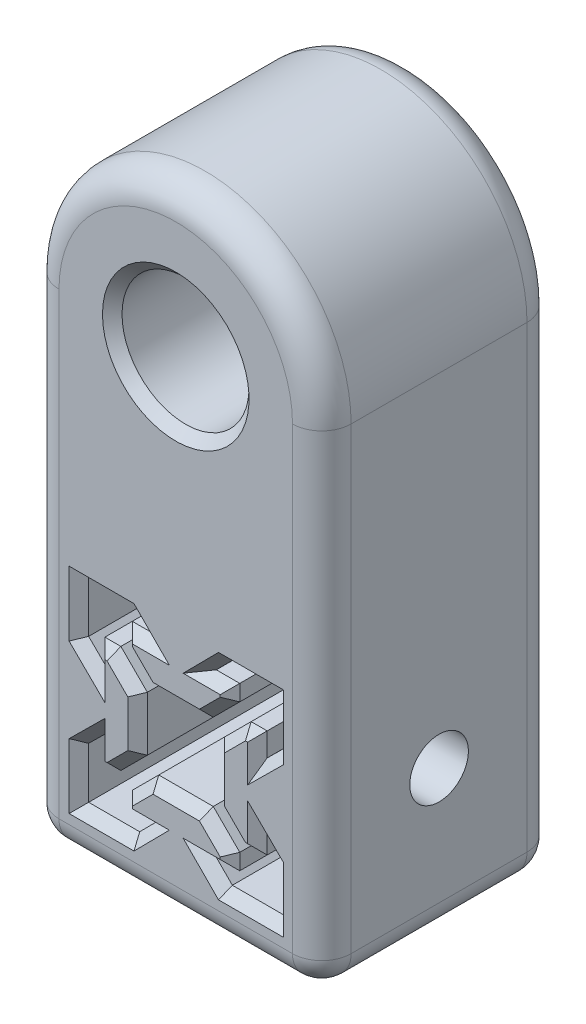
SolidWorks part; units mm, degrees
ref_plane "Front Plane" through (0, 0, 0) normal (0, 0, 1) x (1, 0, 0)
ref_plane "Top Plane" through (0, 0, 0) normal (0, 1, 0) x (1, 0, 0)
ref_plane "Right Plane" through (0, 0, 0) normal (1, 0, 0) x (0, 0, -1)
sketch "Sketch1" plane through (0, 0, 0) normal (0, 0, 1) x (1, 0, 0)
  line L0 (0, -15) -> (0, 15) construction
  line L1 (0, 15) -> (14.8993, 15)
  line L2 (14.8993, 15) -> (14.8993, -14.9496)
  line L3 (14.8993, -14.9496) -> (-15, -14.9496)
  line L4 (-15, -14.9496) -> (-15, 15)
  line L5 (-15, 15) -> (0, 15)
  line L6 (0, -9.9664) -> (0, 9.9664) construction
  line L7 (0, 9.9664) -> (-9.9664, 9.9664) construction
  line L8 (-9.9664, 9.9664) -> (-4.7414, 9.9664)
  line L9 (-4.7414, 9.9664) -> (-3.1, 8.3075)
  line L10 (-3.1, 8.3075) -> (0, 8.3075) construction
  line L11 (-3.1, 8.3075) -> (-5.5, 8.3075)
  line L12 (-5.5, 8.3075) -> (-5.5, 6.6675)
  line L13 (-5.5, 6.6675) -> (-2.79, 3.9575)
  line L14 (-2.79, 3.9575) -> (0, 3.9575) construction
  line L15 (-2.79, 3.9575) -> (2.79, 3.9575)
  line L16 (-9.9664, 9.9664) -> (0, 0) construction
  line L17 (-3.9575, 2.79) -> (-3.9575, -2.79)
  line L18 (-6.6675, 5.5) -> (-3.9575, 2.79)
  line L19 (-8.3075, 5.5) -> (-6.6675, 5.5)
  line L20 (-8.3075, 3.1) -> (-8.3075, 5.5)
  line L21 (-9.9664, 4.7414) -> (-8.3075, 3.1)
  line L22 (-9.9664, 9.9664) -> (-9.9664, 4.7414)
  line L23 (0, 0) -> (-11.0308, 0) construction
  line L24 (5.5, 6.6675) -> (2.79, 3.9575)
  line L25 (5.5, 8.3075) -> (5.5, 6.6675)
  line L26 (3.1, 8.3075) -> (5.5, 8.3075)
  line L27 (4.7414, 9.9664) -> (3.1, 8.3075)
  line L28 (9.9664, 9.9664) -> (4.7414, 9.9664)
  line L29 (9.9664, 9.9664) -> (9.9664, 4.7414)
  line L30 (9.9664, 4.7414) -> (8.3075, 3.1)
  line L31 (8.3075, 3.1) -> (8.3075, 5.5)
  line L32 (8.3075, 5.5) -> (6.6675, 5.5)
  line L33 (6.6675, 5.5) -> (3.9575, 2.79)
  line L34 (3.9575, 2.79) -> (3.9575, -2.79)
  line L35 (-9.9664, -9.9664) -> (0, 0) construction
  line L36 (-2.79, -3.9575) -> (0, -3.9575) construction
  line L37 (-3.1, -8.3075) -> (0, -8.3075) construction
  line L38 (0, -9.9664) -> (-9.9664, -9.9664) construction
  line L39 (6.6675, -5.5) -> (3.9575, -2.79)
  line L40 (8.3075, -5.5) -> (6.6675, -5.5)
  line L41 (8.3075, -3.1) -> (8.3075, -5.5)
  line L42 (9.9664, -4.7414) -> (8.3075, -3.1)
  line L43 (9.9664, -9.9664) -> (9.9664, -4.7414)
  line L44 (9.9664, -9.9664) -> (4.7414, -9.9664)
  line L45 (4.7414, -9.9664) -> (3.1, -8.3075)
  line L46 (3.1, -8.3075) -> (5.5, -8.3075)
  line L47 (5.5, -8.3075) -> (5.5, -6.6675)
  line L48 (5.5, -6.6675) -> (2.79, -3.9575)
  line L49 (-9.9664, -9.9664) -> (-9.9664, -4.7414)
  line L50 (-9.9664, -4.7414) -> (-8.3075, -3.1)
  line L51 (-8.3075, -3.1) -> (-8.3075, -5.5)
  line L52 (-8.3075, -5.5) -> (-6.6675, -5.5)
  line L53 (-6.6675, -5.5) -> (-3.9575, -2.79)
  line L54 (-2.79, -3.9575) -> (2.79, -3.9575)
  line L55 (-5.5, -6.6675) -> (-2.79, -3.9575)
  line L56 (-5.5, -8.3075) -> (-5.5, -6.6675)
  line L57 (-3.1, -8.3075) -> (-5.5, -8.3075)
  line L58 (-4.7414, -9.9664) -> (-3.1, -8.3075)
  line L59 (-9.9664, -9.9664) -> (-4.7414, -9.9664)
  point P43 (3.9575, 0)
  point P58 (-3.9575, 0)
  dimension "D1" = 3.1
  dimension "D2" = 2.79
  dimension "D3" = 2.4
  dimension "D4" = 135
  dimension "D5" = 1.64
  dimension "D6" = 15
  dimension "D7" = 15
  dimension "D8" = 9.9664
  dimension "D9" = 5.225
extrude "Boss-Extrude1" add sketch "Sketch1" along normal blind 24
sketch "Sketch4" plane through (0, 0, 0) normal (0, 0, -1) x (-1, 0, 0)
  line L0 (0.0504, 15) -> (0.0504, 28.5) construction
  line L1 (-14.8993, 15) -> (15, 15) construction
  line L2 (0.0504, 28.5) -> (0.0504, 35) construction
  line L3 (-14.8993, 15) -> (-14.8993, 35)
  line L4 (15, 35) -> (15, 15)
  line L5 (15, 15) -> (-14.8993, 15)
  line L6 (15, -14.9496) -> (-14.8993, -14.9496) construction
  circle A0 centre (0.0504, 35) radius 6.5
  arc A1 (-14.8993, 35) -> (15, 35) centre (0.0504, 35) cw
  line M2 (15, 15) -> (-14.8993, 15)
  dimension "D2" = 13
  dimension "D3" = 14.9496
  dimension "D1" = 29.9496
  dimension "D4" = 13.5
extrude "Boss-Extrude2" add sketch "Sketch4" against normal up to surface (24 mm away) contours A1 L3 L4 A0 M2
sketch "Sketch3" plane through (-15, 0, 0) normal (-1, 0, 0) x (0, 0, 1)
  line L0 (12, 0) -> (24, 10.0252) construction
  line L2 (0, 0) -> (12, 0) construction
  line L3 (24, 35) -> (24, -14.9496) construction
  circle A0 centre (12, 0) radius 3
extrude "Cut-Extrude1" cut sketch "Sketch3" against normal through all
fillet "Fillet1" radius 3 10 edges at (-0.0504, -14.9496, 24) (14.8993, 10.0252, 24) (-15, 10.0252, 24) (14.8993, 10.0252, 0) (-15, 10.0252, 0) (-0.0504, -14.9496, 0) (14.8993, -14.9496, 12) (-15, -14.9496, 12) (-0.0504, 49.9496, 24) (-0.0504, 49.9496, 0)
chamfer "Chamfer1" distance 1 angle 45 90 edges at (-6.5504, 35, 0) (-4.145, 5.3125, 0) (0, 3.9575, 0) (4.145, 5.3125, 0) (5.5, 7.4875, 0) (4.3, 8.3075, 0) (3.9207, 9.1369, 0) (7.3539, 9.9664, 0) (9.9664, 7.3539, 0) (9.1369, 3.9207, 0) (8.3075, 4.3, 0) (7.4875, 5.5, 0) (5.3125, 4.145, 0) (3.9575, 0, 0) (5.3125, -4.145, 0) (7.4875, -5.5, 0) (8.3075, -4.3, 0) (9.1369, -3.9207, 0) (9.9664, -7.3539, 0) (7.3539, -9.9664, 0) (3.9207, -9.1369, 0) (4.3, -8.3075, 0) (5.5, -7.4875, 0) (4.145, -5.3125, 0) (0, -3.9575, 0) (-4.145, -5.3125, 0) (-5.5, -7.4875, 0) (-4.3, -8.3075, 0) (-3.9207, -9.1369, 0) (-7.3539, -9.9664, 0) (-9.9664, -7.3539, 0) (-9.1369, -3.9207, 0) (-8.3075, -4.3, 0) (-7.4875, -5.5, 0) (-5.3125, -4.145, 0) (-3.9575, 0, 0) (-5.3125, 4.145, 0) (-7.4875, 5.5, 0) (-8.3075, 4.3, 0) (-9.1369, 3.9207, 0) (-9.9664, 7.3539, 0) (-7.3539, 9.9664, 0) (-3.9207, 9.1369, 0) (-4.3, 8.3075, 0) (-5.5, 7.4875, 0) (-6.5504, 35, 24) (-3.9207, 9.1369, 24) (-7.3539, 9.9664, 24) (-9.9664, 7.3539, 24) (-9.1369, 3.9207, 24) (-8.3075, 4.3, 24) (-7.4875, 5.5, 24) (-5.3125, 4.145, 24) (-3.9575, 0, 24) (-5.3125, -4.145, 24) (-7.4875, -5.5, 24) (-8.3075, -4.3, 24) (-9.1369, -3.9207, 24) (-9.9664, -7.3539, 24) (-7.3539, -9.9664, 24) (-3.9207, -9.1369, 24) (-4.3, -8.3075, 24) (-5.5, -7.4875, 24) (-4.145, -5.3125, 24) (0, -3.9575, 24) (4.145, -5.3125, 24) (5.5, -7.4875, 24) (4.3, -8.3075, 24) (3.9207, -9.1369, 24) (7.3539, -9.9664, 24) (9.9664, -7.3539, 24) (9.1369, -3.9207, 24) (8.3075, -4.3, 24) (7.4875, -5.5, 24) (5.3125, -4.145, 24) (3.9575, 0, 24) (5.3125, 4.145, 24) (7.4875, 5.5, 24) (8.3075, 4.3, 24) (9.1369, 3.9207, 24) (9.9664, 7.3539, 24) (7.3539, 9.9664, 24) (3.9207, 9.1369, 24) (4.3, 8.3075, 24) (5.5, 7.4875, 24) (4.145, 5.3125, 24) (0, 3.9575, 24) (-4.145, 5.3125, 24) (-5.5, 7.4875, 24) (-4.3, 8.3075, 24)
